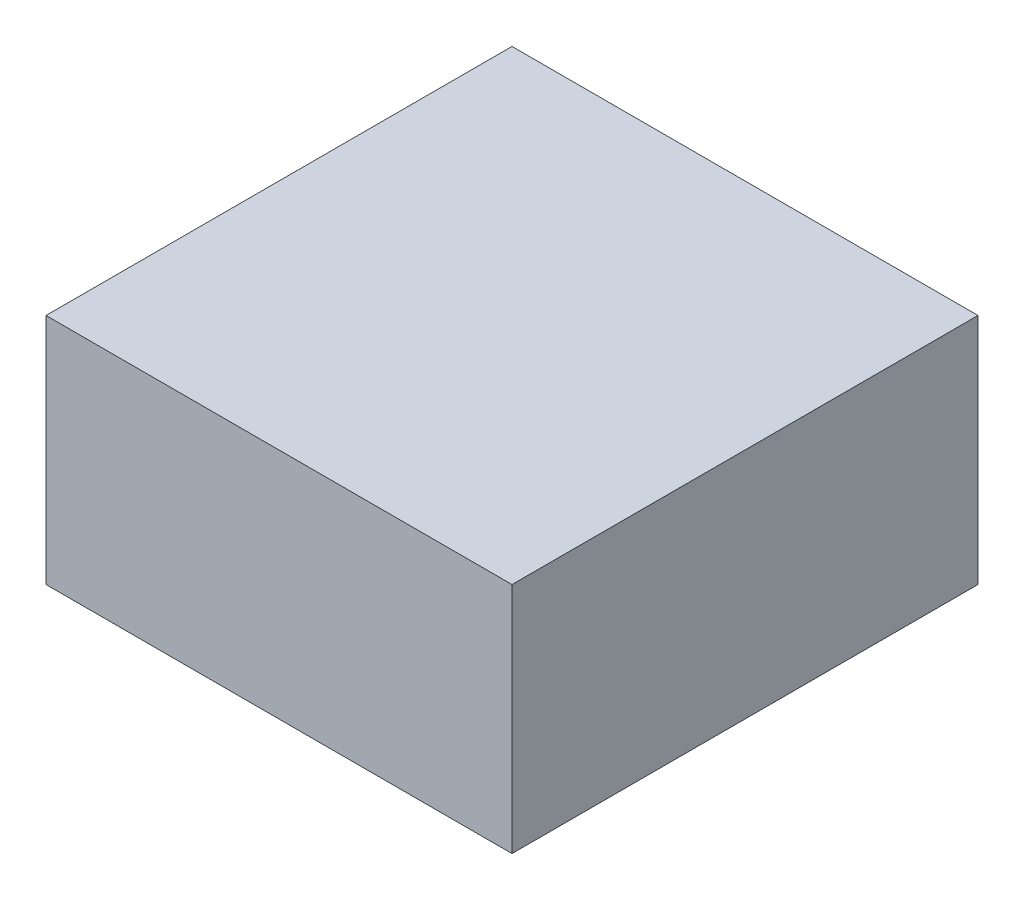
SolidWorks part; units mm, degrees
ref_plane "Front Plane" through (0, 0, 0) normal (0, 0, 1) x (1, 0, 0)
ref_plane "Top Plane" through (0, 0, 0) normal (0, 1, 0) x (1, 0, 0)
ref_plane "Right Plane" through (0, 0, 0) normal (1, 0, 0) x (0, 0, -1)
sketch "Sketch1" plane through (0, 0, 0) normal (0, 1, 0) x (1, 0, 0)
  line L1 (0.1, 0.1) -> (-0.1, 0.1)
  line L2 (0.1, 0.1) -> (0.1, -0.1)
  line L3 (0.1, -0.1) -> (-0.1, -0.1)
  line L4 (-0.1, 0.1) -> (-0.1, -0.1)
extrude "Boss-Extrude1" add sketch "Sketch1" along normal blind 0.1
